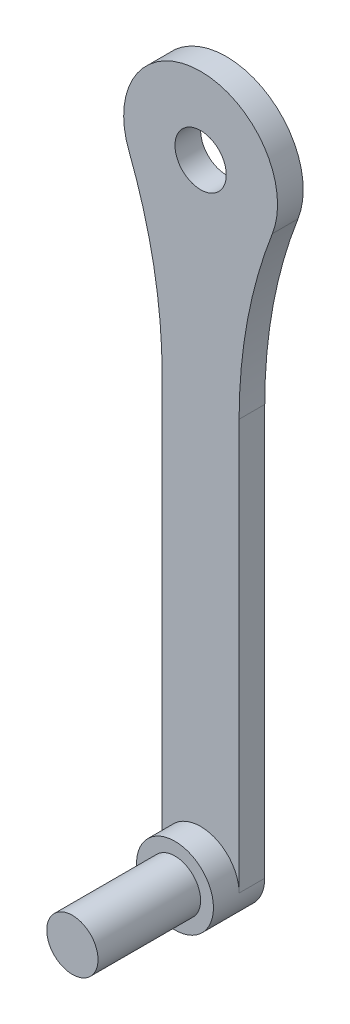
SolidWorks part; units mm, degrees
ref_plane "Front Plane" through (0, 0, 0) normal (0, 0, 1) x (1, 0, 0)
ref_plane "Top Plane" through (0, 0, 0) normal (0, 1, 0) x (1, 0, 0)
ref_plane "Right Plane" through (0, 0, 0) normal (1, 0, 0) x (0, 0, -1)
ref_plane "Plane1" through (0, 0, 0) normal (0, 0, -1) x (-1, 0, 0)
sketch "Sketch1" plane through (0, 0, 0) normal (0, 0, -1) x (-1, 0, 0)
  line L0 (7.5, -120) -> (7.5, -12.9904)
  line L1 (-7.5, -12.9904) -> (-7.5, -120)
  arc A0 (7.5, -12.9904) -> (-7.5, -12.9904) centre (0, 0) ccw
  arc A1 (-7.5, -120) -> (7.5, -120) centre (0, -120) ccw
extrude "Boss-Extrude1" add sketch "Sketch1" against normal blind 5
sketch "Sketch2" plane through (0, 0, 5) normal (0, 0, 1) x (1, 0, 0)
  circle A0 centre (0, -120) radius 7.5
extrude "Boss-Extrude2" add sketch "Sketch2" along normal blind 5
sketch "Sketch3" plane through (0, 0, 10) normal (0, 0, 1) x (1, 0, 0)
  circle A0 centre (0, -120) radius 5
extrude "Boss-Extrude3" add sketch "Sketch3" along normal blind 20
hole_wizard "Ø10.0 (10) Diameter Hole1" positions "Sketch5" profile "Sketch4" hole size "Ø10.0" standard "ANSI Metric"
sketch "Sketch5" plane through (0, 0, 0) normal (0, 0, -1) x (-1, 0, 0)
  point P0 (0, 0)
sketch "Sketch4" plane through (0, 0, 0) normal (1, 0, 0) x (0, 1, 0)
  line L0 (0, 0) -> (0, 30)
  line L1 (0, 30) -> (5, 30)
  line L2 (5, 30) -> (5, 0)
  line L5 (5, 0) -> (0, 0)
  line L11 (0, -6.35) -> (0, 107.95) construction
  dimension "Thru Hole Dia." = 10
  dimension "Thru Hole Depth" = 30
fillet "Fillet1" radius 95.4167 2 edges at (-7.5, -12.9904, 2.5) (7.5, -12.9904, 2.5)
